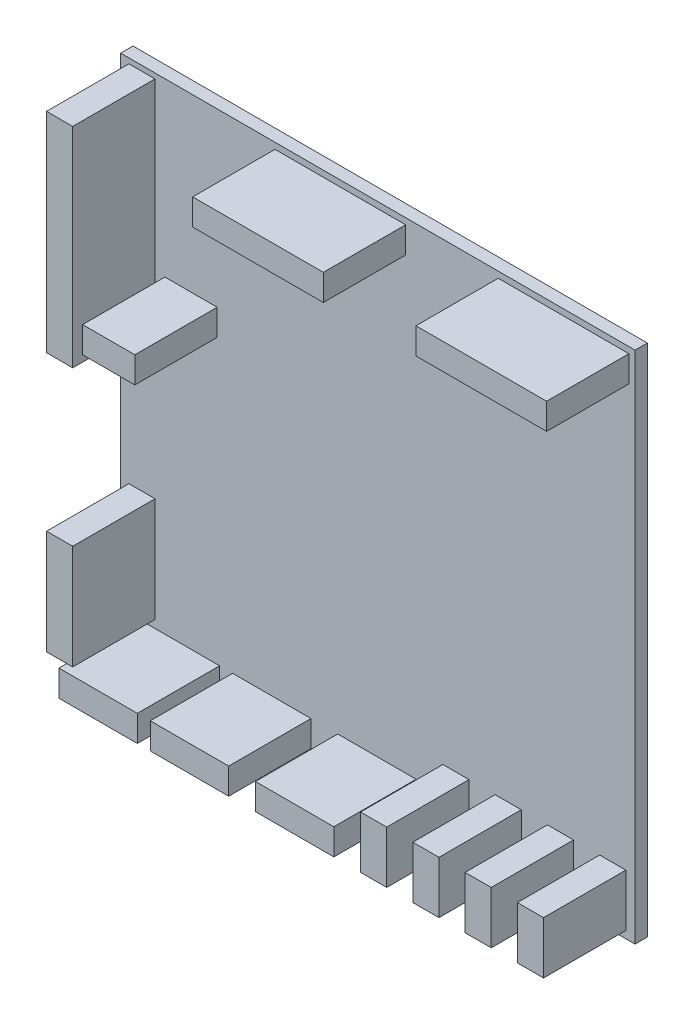
SolidWorks part; units mm, degrees
ref_plane "Alzado" through (0, 0, 0) normal (0, 0, 1) x (1, 0, 0)
ref_plane "Planta" through (0, 0, 0) normal (0, 1, 0) x (1, 0, 0)
ref_plane "Vista lateral" through (0, 0, 0) normal (1, 0, 0) x (0, 0, -1)
sketch "Croquis1" plane through (0, 0, 0) normal (0, 0, 1) x (1, 0, 0)
  line L1 (0, 0) -> (50, 0)
  line L2 (0, 0) -> (0, 50)
  line L3 (0, 50) -> (50, 50)
  line L4 (50, 0) -> (50, 50)
  dimension "D1" = 50
  dimension "D2" = 50
extrude "Saliente-Extruir1" add sketch "Croquis1" along normal blind 1.2
sketch "Croquis2" plane through (0, 0, 1.2) normal (0, 0, 1) x (1, 0, 0)
  line L0 (50, 0) -> (50, 50) construction
  line L1 (49.4, 49.4) -> (36.7, 49.4)
  line L2 (49.4, 49.4) -> (49.4, 46.86)
  line L3 (49.4, 46.86) -> (36.7, 46.86)
  line L4 (36.7, 49.4) -> (36.7, 46.86)
  line L5 (27.7, 49.4) -> (15, 49.4)
  line L6 (27.7, 49.4) -> (27.7, 46.86)
  line L7 (27.7, 46.86) -> (15, 46.86)
  line L8 (15, 49.4) -> (15, 46.86)
  line L9 (0.8, 49.5) -> (3.34, 49.5)
  line L10 (0.8, 49.5) -> (0.8, 29.18)
  line L11 (0.8, 29.18) -> (3.34, 29.18)
  line L12 (3.34, 49.5) -> (3.34, 29.18)
  line L13 (4.3, 33.3) -> (9.38, 33.3)
  line L14 (4.3, 33.3) -> (4.3, 30.76)
  line L15 (4.3, 30.76) -> (9.38, 30.76)
  line L16 (9.38, 33.3) -> (9.38, 30.76)
  line L17 (0.8, 14.16) -> (3.34, 14.16)
  line L18 (0.8, 14.16) -> (0.8, 4)
  line L19 (0.8, 4) -> (3.34, 4)
  line L20 (3.34, 14.16) -> (3.34, 4)
  line L21 (2, 3.24) -> (9.62, 3.24)
  line L22 (2, 3.24) -> (2, 0.7)
  line L23 (2, 0.7) -> (9.62, 0.7)
  line L24 (9.62, 3.24) -> (9.62, 0.7)
  line L25 (10.88, 3.24) -> (18.5, 3.24)
  line L26 (10.88, 3.24) -> (10.88, 0.7)
  line L27 (10.88, 0.7) -> (18.5, 0.7)
  line L28 (18.5, 3.24) -> (18.5, 0.7)
  line L29 (21.1, 3.24) -> (28.72, 3.24)
  line L30 (21.1, 3.24) -> (21.1, 0.7)
  line L31 (21.1, 0.7) -> (28.72, 0.7)
  line L32 (28.72, 3.24) -> (28.72, 0.7)
  line L33 (31.32, 5.78) -> (33.86, 5.78)
  line L34 (31.32, 5.78) -> (31.32, 0.7)
  line L35 (31.32, 0.7) -> (33.86, 0.7)
  line L36 (33.86, 5.78) -> (33.86, 0.7)
  line L37 (36.4, 5.78) -> (38.94, 5.78)
  line L38 (36.4, 5.78) -> (36.4, 0.7)
  line L39 (36.4, 0.7) -> (38.94, 0.7)
  line L40 (38.94, 5.78) -> (38.94, 0.7)
  line L41 (41.48, 5.78) -> (44.02, 5.78)
  line L42 (41.48, 5.78) -> (41.48, 0.7)
  line L43 (41.48, 0.7) -> (44.02, 0.7)
  line L44 (44.02, 5.78) -> (44.02, 0.7)
  line L45 (46.56, 5.78) -> (49.1, 5.78)
  line L46 (46.56, 5.78) -> (46.56, 0.7)
  line L47 (46.56, 0.7) -> (49.1, 0.7)
  line L48 (49.1, 5.78) -> (49.1, 0.7)
  line L49 (50, 50) -> (0, 50) construction
  line L50 (0, 50) -> (0, 0) construction
  line L51 (0, 0) -> (50, 0) construction
  dimension "D1" = 2.54
  dimension "D2" = 12.7
  dimension "D3" = 9
  dimension "D4" = 0.6
  dimension "D5" = 0.6
  dimension "D6" = 0.8
  dimension "D7" = 0.5
  dimension "D8" = 20.32
  dimension "D9" = 10.16
  dimension "D10" = 5.08
  dimension "D11" = 7.62
  dimension "D12" = 0.9
  dimension "D13" = 2.54
  dimension "D14" = 2.54
  dimension "D15" = 2.54
  dimension "D16" = 2.6
  dimension "D17" = 2.6
  dimension "D18" = 2
  dimension "D19" = 0.7
  dimension "D20" = 4
  dimension "D21" = 16.7
  dimension "D22" = 4.3
extrude "Saliente-Extruir2" add sketch "Croquis2" along normal blind 8
